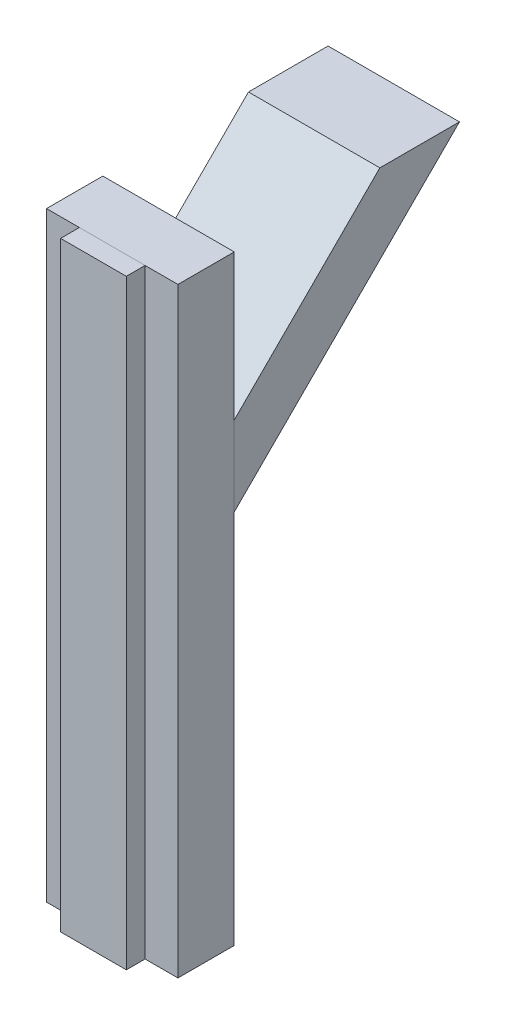
SolidWorks part; units mm, degrees
ref_plane "Front Plane" through (0, 0, 0) normal (0, 0, 1) x (1, 0, 0)
ref_plane "Top Plane" through (0, 0, 0) normal (0, 1, 0) x (1, 0, 0)
ref_plane "Right Plane" through (0, 0, 0) normal (1, 0, 0) x (0, 0, -1)
sketch "Sketch2" plane through (0, 0, 0) normal (1, 0, 0) x (0, 0, -1)
  line L1 (-19.05, 0) -> (19.05, 0)
  line L2 (-19.05, 0) -> (-19.05, -406.4)
  line L3 (-19.05, -406.4) -> (19.05, -406.4)
  line L4 (19.05, 0) -> (19.05, -406.4)
  dimension "D1" = 406.4
  dimension "D2" = 38.1
extrude "Slider_Board" add sketch "Sketch2" along normal blind 88.9
sketch "Sketch3" plane through (0, 0, 0) normal (1, 0, 0) x (0, 0, -1)
  line L0 (19.05, -152.4) -> (171.45, 0)
  line L1 (19.05, -406.4) -> (19.05, 0) construction
  line L2 (19.05, -98.5185) -> (117.5685, 0)
  line L3 (20.955, 0) -> (-20.955, 0) construction
  line L5 (117.5685, 0) -> (171.45, 0)
  line L6 (19.05, -98.5185) -> (19.05, -152.4)
  dimension "D1" = 38.1
  dimension "D2" = 152.4
extrude "Diagonal_Support" add sketch "Sketch3" along normal blind 88.9 separate body
sketch "Sketch4" plane through (0, 0, 19.05) normal (0, 0, 1) x (1, 0, 0)
  line L0 (88.9, 0) -> (0, 0) construction
  line L1 (66.675, 0) -> (22.225, 0)
  line L2 (66.675, 0) -> (66.675, -406.4)
  line L3 (66.675, -406.4) -> (22.225, -406.4)
  line L4 (22.225, 0) -> (22.225, -406.4)
  point P6 (44.45, 0)
  dimension "D1" = 44.45
  dimension "D2" = 406.4
extrude "Slider" add sketch "Sketch4" along normal blind 12.7 separate body
